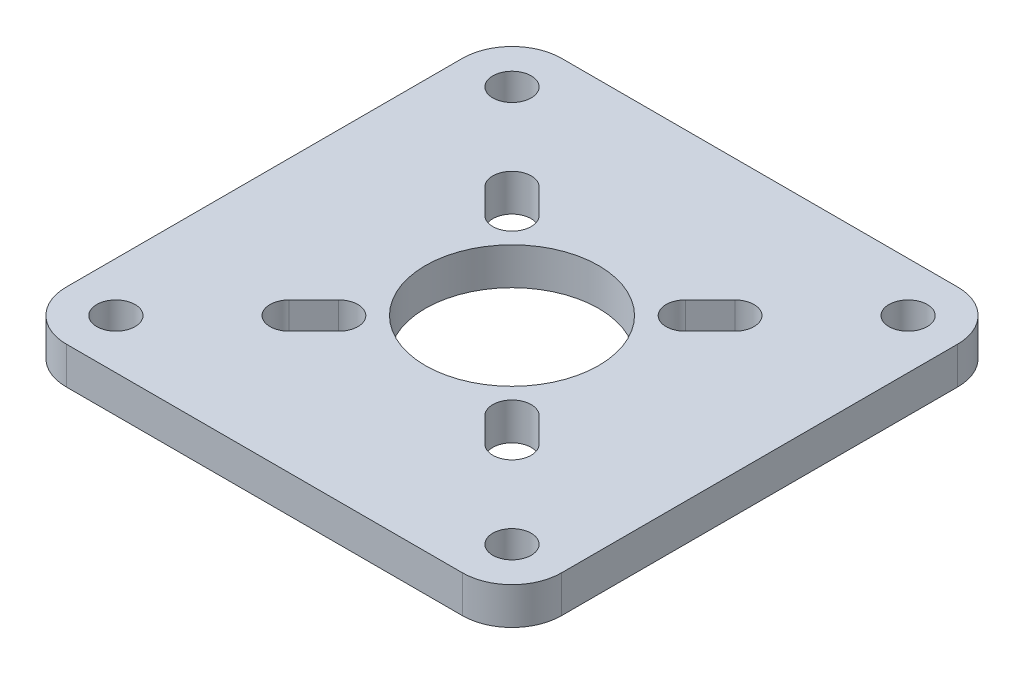
SolidWorks part; units mm, degrees
ref_plane "Front Plane" through (0, 0, 0) normal (0, 0, 1) x (1, 0, 0)
ref_plane "Top Plane" through (0, 0, 0) normal (0, 1, 0) x (1, 0, 0)
ref_plane "Right Plane" through (0, 0, 0) normal (1, 0, 0) x (0, 0, -1)
sketch "Sketch1" plane through (0, 0, 0) normal (0, 1, 0) x (1, 0, 0)
  line L1 (-20, -20) -> (20, -20)
  line L2 (-20, -20) -> (-20, 20)
  line L3 (-20, 20) -> (20, 20)
  line L4 (20, -20) -> (20, 20)
  line L5 (-20, -20) -> (20, 20) construction
  line L6 (-20, 20) -> (20, -20) construction
  point P0 (0, 0)
  dimension "D1" = 40
extrude "Boss-Extrude1" add sketch "Sketch1" along normal mid plane 3
fillet "Fillet1" radius 4 4 edges at (-20, 0, 20) (20, 0, 20) (20, 0, -20) (-20, 0, -20)
sketch "Sketch3" plane through (0, 1.5, 0) normal (0, 1, 0) x (1, 0, 0)
  line L2 (7, -7) -> (9, -9) construction
  line L3 (8.096, -5.904) -> (10.096, -7.904)
  line L4 (5.904, -8.096) -> (7.904, -10.096)
  line L5 (0, 0) -> (-3.2468, 0) construction
  line L6 (-6, 6) -> (6, 6)
  line L7 (-6, 6) -> (-6, -6)
  line L8 (-6, -6) -> (6, -6)
  line L9 (6, 6) -> (6, -6)
  line L10 (-6, 6) -> (6, -6) construction
  line L11 (-6, -6) -> (6, 6) construction
  line L12 (0, 0) -> (0, 3.3382) construction
  line L13 (7, 7) -> (9, 9) construction
  line L14 (8.096, 5.904) -> (10.096, 7.904)
  line L15 (5.904, 8.096) -> (7.904, 10.096)
  line L16 (-7, -7) -> (-9, -9) construction
  line L17 (-8.096, -5.904) -> (-10.096, -7.904)
  line L18 (-5.904, -8.096) -> (-7.904, -10.096)
  line L19 (-7, 7) -> (-9, 9) construction
  line L20 (-8.096, 5.904) -> (-10.096, 7.904)
  line L21 (-5.904, 8.096) -> (-7.904, 10.096)
  line L23 (-16, -20) -> (16, -20) construction
  circle A0 centre (0, 0) radius 7
  circle A1 centre (16, -16) radius 1.55
  arc A3 (8.096, -5.904) -> (5.904, -8.096) centre (7, -7) ccw
  arc A4 (7.904, -10.096) -> (10.096, -7.904) centre (9, -9) ccw
  circle A5 centre (16, 16) radius 1.55
  arc A6 (8.096, 5.904) -> (5.904, 8.096) centre (7, 7) cw
  arc A7 (7.904, 10.096) -> (10.096, 7.904) centre (9, 9) cw
  circle A8 centre (-16, -16) radius 1.55
  arc A9 (-8.096, -5.904) -> (-5.904, -8.096) centre (-7, -7) cw
  arc A10 (-7.904, -10.096) -> (-10.096, -7.904) centre (-9, -9) cw
  circle A11 centre (-16, 16) radius 1.55
  arc A12 (-8.096, 5.904) -> (-5.904, 8.096) centre (-7, 7) ccw
  arc A13 (-7.904, 10.096) -> (-10.096, 7.904) centre (-9, 9) ccw
  point P5 (14.821, -16.2585)
  point P6 (0, 0)
  point P11 (8, -8)
  point P18 (0, 0)
  point P27 (8, 8)
  point P36 (-8, -8)
  point P45 (-8, 8)
  dimension "D1" = 14
  dimension "D2" = 3.1
  dimension "D7" = 18
  dimension "D3" = 4
  dimension "D5" = 7
  dimension "D6" = 12
extrude "Cut-Extrude2" cut sketch "Sketch3" against normal up to surface (3 mm away) contours A0 | L4 A4 L3 A3 | A1 | A10 L18 A9 L17 | L21 A13 L20 A12 | A11 | A7 L15 A6 L14 | A5 | A8 | L7 A12 L6 | A9 L7 L8 | L9 A3 L8 | A6 L9 L6 | L7 A0 | L6 A0 | L9 A0 | L8 A0 up to face at (0, -1.5, 0)
